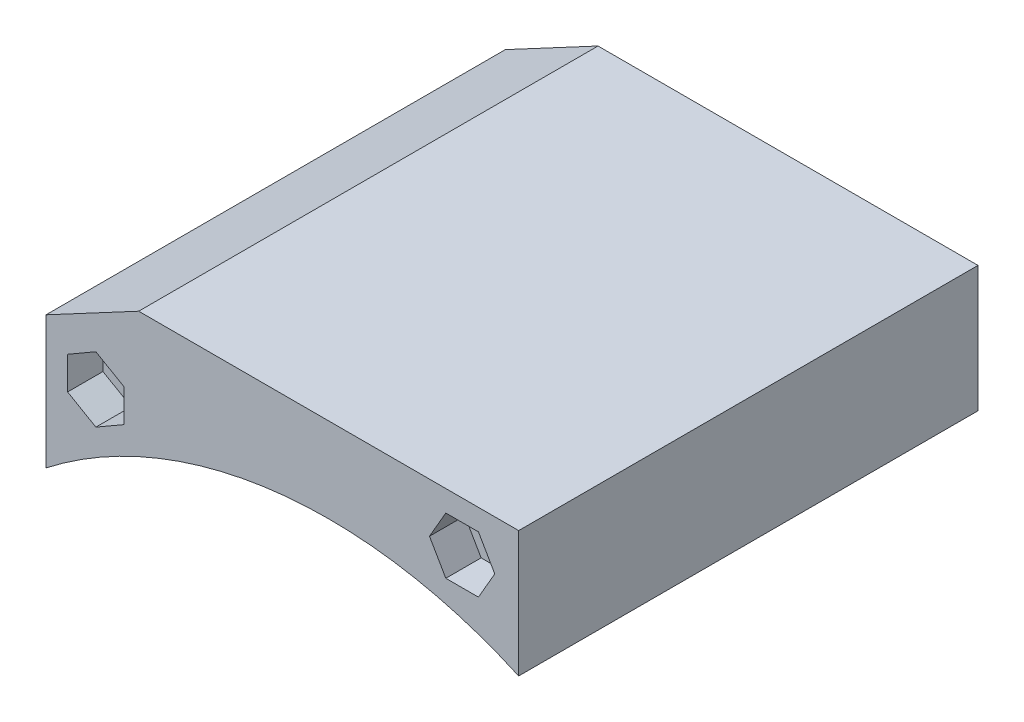
SolidWorks part; units mm, degrees
ref_plane "Front Plane" through (0, 0, 0) normal (0, 0, 1) x (1, 0, 0)
ref_plane "Top Plane" through (0, 0, 0) normal (0, 1, 0) x (1, 0, 0)
ref_plane "Right Plane" through (0, 0, 0) normal (1, 0, 0) x (0, 0, -1)
sketch "Sketch1" plane through (0, 0, 0) normal (0, 0, 1) x (1, 0, 0)
  line L0 (-26.885, 0) -> (26.885, 0)
  line L1 (0, 0) -> (0, -7) construction
  line L2 (0, -7) -> (-40, -7) construction
  line L3 (-26.885, 0) -> (-40, -7)
  line L4 (0, -7) -> (0, -77) construction
  line L5 (-40, -7) -> (-40, -25.7652)
  line L6 (26.885, 0) -> (26.885, -17.8206)
  arc A0 (26.885, -17.8206) -> (-40, -25.7652) centre (0, -77) ccw
  point P4 (0, 0)
  dimension "D5" = 130
  dimension "D1" = 53.77
  dimension "D2" = 7
  dimension "D3" = 40
  dimension "D4" = 70
extrude "Boss-Extrude1" add sketch "Sketch1" along normal blind 65
sketch "Sketch2" plane through (0, 0, 65) normal (0, 0, 1) x (1, 0, 0)
  line L0 (-40, -16.3826) -> (-32.9424, -12.6157) construction
  line L1 (-40, -7) -> (-40, -25.7652) construction
  line L2 (-26.885, 0) -> (-40, -7) construction
  line L3 (26.885, -7) -> (18.885, -7) construction
  line L4 (-32.9424, -17.2345) -> (-28.9424, -14.9251)
  line L5 (-28.9424, -14.9251) -> (-28.9424, -10.3063)
  line L6 (-28.9424, -10.3063) -> (-32.9424, -7.9969)
  line L7 (-32.9424, -7.9969) -> (-36.9424, -10.3063)
  line L8 (-36.9424, -10.3063) -> (-36.9424, -14.9251)
  line L9 (-36.9424, -14.9251) -> (-32.9424, -17.2345)
  line L11 (26.885, 0) -> (-26.885, 0) construction
  line L12 (14.2662, -7) -> (16.5756, -11)
  line L13 (16.5756, -11) -> (21.1944, -11)
  line L14 (21.1944, -11) -> (23.5038, -7)
  line L15 (23.5038, -7) -> (21.1944, -3)
  line L16 (21.1944, -3) -> (16.5756, -3)
  line L17 (16.5756, -3) -> (14.2662, -7)
  circle A0 centre (-32.9424, -12.6157) radius 4 construction
  circle A1 centre (18.885, -7) radius 4 construction
  point P17 (0, 0)
  dimension "D1" = 8
  dimension "D2" = 8
  dimension "D3" = 8
  dimension "D4" = 8
  dimension "D5" = 7
extrude "Cut-Extrude1" cut sketch "Sketch2" against normal blind 5
sketch "Sketch3" plane through (0, 0, 0) normal (0, 0, -1) x (-1, 0, 0)
  line L0 (40, -16.3826) -> (32.9424, -12.6157) construction
  line L1 (40, -7) -> (40, -25.7652) construction
  line L2 (26.885, 0) -> (40, -7) construction
  line L3 (-26.885, -7) -> (-18.885, -7) construction
  line L4 (28.8619, -10.4517) -> (29.0281, -15.0675)
  line L5 (29.0281, -15.0675) -> (33.1086, -17.2315)
  line L6 (33.1086, -17.2315) -> (37.0229, -14.7796)
  line L7 (37.0229, -14.7796) -> (36.8567, -10.1638)
  line L8 (36.8567, -10.1638) -> (32.7762, -7.9999)
  line L9 (32.7762, -7.9999) -> (28.8619, -10.4517)
  line L10 (-26.885, -17.8206) -> (-26.885, 0) construction
  line L11 (-26.885, 0) -> (26.885, 0) construction
  line L13 (-16.5261, -10.971) -> (-14.2666, -6.9426)
  line L14 (-14.2666, -6.9426) -> (-16.6255, -2.9716)
  line L15 (-16.6255, -2.9716) -> (-21.2439, -3.029)
  line L16 (-21.2439, -3.029) -> (-23.5034, -7.0574)
  line L17 (-23.5034, -7.0574) -> (-21.1445, -11.0284)
  line L18 (-21.1445, -11.0284) -> (-16.5261, -10.971)
  circle A0 centre (32.9424, -12.6157) radius 4 construction
  circle A1 centre (-18.885, -7) radius 4 construction
  dimension "D1" = 8
  dimension "D2" = 8
  dimension "D3" = 7
  dimension "D4" = 8
  dimension "D5" = 8
extrude "Cut-Extrude2" cut sketch "Sketch3" against normal blind 5
sketch "Sketch4" plane through (0, 0, 5) normal (0, 0, -1) x (-1, 0, 0)
  line L0 (-18.9347, -3.0003) -> (-18.8353, -10.9997) construction
  line L1 (-16.6255, -2.9716) -> (-21.2439, -3.029) construction
  line L2 (-21.1445, -11.0284) -> (-16.5261, -10.971) construction
  line L3 (28.945, -12.7596) -> (36.9398, -12.4717) construction
  line L4 (28.8619, -10.4517) -> (29.0281, -15.0675) construction
  line L5 (37.0229, -14.7796) -> (36.8567, -10.1638) construction
  circle A0 centre (32.9424, -12.6157) radius 2.1
  circle A1 centre (-18.885, -7) radius 2.1
  dimension "D1" = 4.2
extrude "Cut-Extrude3" cut sketch "Sketch4" against normal blind 10
sketch "Sketch5" plane through (0, 0, 60) normal (0, 0, 1) x (1, 0, 0)
  line L0 (-36.9424, -12.6157) -> (-28.9424, -12.6157) construction
  line L1 (-36.9424, -10.3063) -> (-36.9424, -14.9251) construction
  line L2 (-28.9424, -14.9251) -> (-28.9424, -10.3063) construction
  line L3 (18.885, -3) -> (18.885, -11) construction
  line L4 (21.1944, -3) -> (16.5756, -3) construction
  line L5 (16.5756, -11) -> (21.1944, -11) construction
  circle A0 centre (-32.9424, -12.6157) radius 2.1
  circle A1 centre (18.885, -7) radius 2.1
  dimension "D1" = 4.2
extrude "Cut-Extrude4" cut sketch "Sketch5" against normal blind 10
